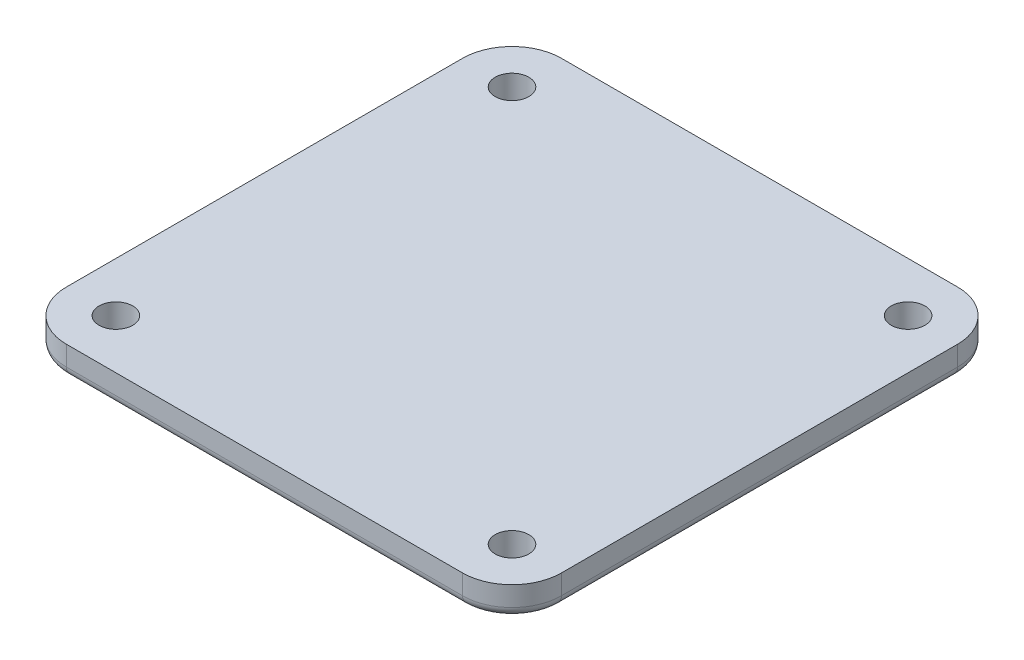
SolidWorks part; units mm, degrees
ref_plane "Front" through (0, 0, 0) normal (0, 0, 1) x (1, 0, 0)
ref_plane "Top" through (0, 0, 0) normal (0, 1, 0) x (1, 0, 0)
ref_plane "Right" through (0, 0, 0) normal (1, 0, 0) x (0, 0, -1)
sketch "Sketch1" plane through (0, -4, 0) normal (0, -1, 0) x (1, 0, 0)
  line L4 (-20, -25) -> (20, -25)
  line L5 (25, -20) -> (25, 20)
  line L6 (20, 25) -> (-20, 25)
  line L7 (-25, 20) -> (-25, -20)
  line L8 (-20, -25) -> (20, -25)
  line L9 (25, -20) -> (25, 20)
  line L10 (20, 25) -> (-20, 25)
  line L11 (-25, 20) -> (-25, -20)
  circle A1 centre (-20, 20) radius 1.7
  circle A2 centre (-20, 20) radius 1.7
  circle A3 centre (20, 20) radius 1.7
  circle A4 centre (20, 20) radius 1.7
  circle A5 centre (-20, -20) radius 1.7
  circle A6 centre (-20, -20) radius 1.7
  circle A7 centre (20, -20) radius 1.7
  circle A8 centre (20, -20) radius 1.7
  arc A12 (-25, -20) -> (-20, -25) centre (-20, -20) ccw
  arc A13 (20, -25) -> (25, -20) centre (20, -20) ccw
  arc A14 (25, 20) -> (20, 25) centre (20, 20) ccw
  arc A15 (-20, 25) -> (-25, 20) centre (-20, 20) ccw
  arc A16 (-25, -20) -> (-20, -25) centre (-20, -20) ccw
  arc A17 (20, -25) -> (25, -20) centre (20, -20) ccw
  arc A18 (25, 20) -> (20, 25) centre (20, 20) ccw
  arc A19 (-20, 25) -> (-25, 20) centre (-20, 20) ccw
  dimension "D1" = 0
  dimension "D2" = 0
  dimension "D3" = 0
  dimension "D4" = 0
  dimension "D5" = 0
extrude "Boss-Extrude1" add sketch "Sketch1" along normal blind 3
fillet "Fillet1" radius 1 8 edges at (-23.5355, -7, -23.5355) (-25, -7, 0) (-23.5355, -7, 23.5355) (0, -7, 25) (23.5355, -7, 23.5355) (25, -7, 0) (23.5355, -7, -23.5355) (0, -7, -25)
